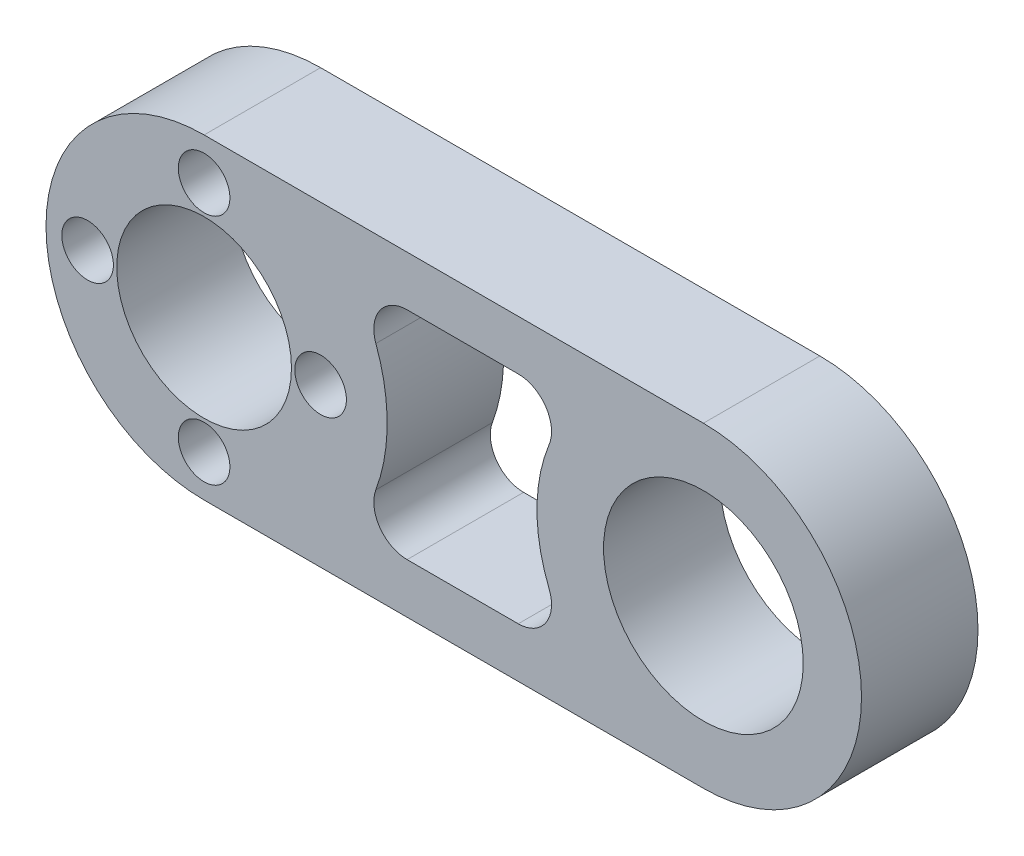
SolidWorks part; units mm, degrees
material "Thornel Mat VMA"
ref_plane "前视基准面" through (0, 0, 0) normal (0, 0, 1) x (1, 0, 0)
ref_plane "上视基准面" through (0, 0, 0) normal (0, 1, 0) x (1, 0, 0)
ref_plane "右视基准面" through (0, 0, 0) normal (1, 0, 0) x (0, 0, -1)
sketch "草图1" plane through (0, 0, 0) normal (0, 0, 1) x (1, 0, 0)
  line L0 (0, 0) -> (30, 0) construction
  line L1 (0, 9.5) -> (30, 9.5)
  line L2 (0, -9.5) -> (30, -9.5)
  line L3 (0, 0) -> (0, -7) construction
  line L4 (0, 6.5) -> (30, 6.5) construction
  line L5 (0, -6.5) -> (30, -6.5) construction
  line L6 (22.4007, -6.5) -> (8.8741, -6.5)
  line L7 (22.4007, 6.5) -> (8.8741, 6.5)
  arc A0 (0, 9.5) -> (0, -9.5) centre (0, 0) ccw
  arc A1 (30, -9.5) -> (30, 9.5) centre (30, 0) ccw
  circle A2 centre (0, 0) radius 5.25
  circle A3 centre (30, 0) radius 6
  circle A4 centre (0, 0) radius 7 construction
  circle A5 centre (0, -7) radius 1.55
  circle A6 centre (-7, 0) radius 1.55
  circle A7 centre (0, 7) radius 1.55
  circle A8 centre (7, 0) radius 1.55
  circle A9 centre (30, 0) radius 10 construction
  circle A10 centre (0, 0) radius 11 construction
  arc A11 (30, -6.5) -> (30, 6.5) centre (30, 0) ccw construction
  arc A12 (0, 6.5) -> (0, -6.5) centre (0, 0) ccw construction
  arc A13 (22.4007, -6.5) -> (22.4007, 6.5) centre (30, 0) cw
  arc A14 (8.8741, -6.5) -> (8.8741, 6.5) centre (0, 0) ccw
  point P3 (15, 0)
  dimension "D1" = 10.5
  dimension "D3" = 9.5
  dimension "D4" = 12
  dimension "D5" = 3.1
  dimension "D8" = 14
  dimension "D2" = 30
  dimension "D7" = 4
  dimension "D9" = 4
  dimension "D10" = 3
  dimension "D6" = 4
extrude "凸台-拉伸1" add sketch "草图1" along normal blind 7
fillet "圆角1" radius 2 4 edges at (8.8741, 6.5, 3.5) (8.8741, -6.5, 3.5) (22.4007, 6.5, 3.5) (22.4007, -6.5, 3.5)
